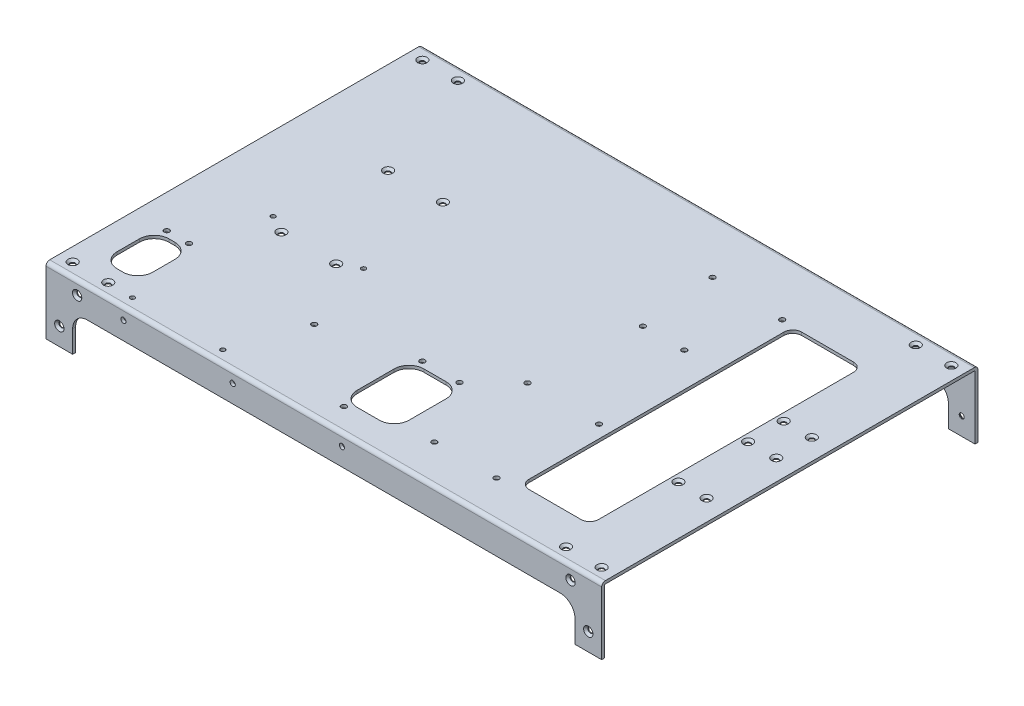
SolidWorks part; units mm, degrees
material "6061-T6 (SS)"
ref_plane "Front Plane" through (0, 0, 0) normal (0, 0, 1) x (1, 0, 0)
ref_plane "Top Plane" through (0, 0, 0) normal (0, 1, 0) x (1, 0, 0)
ref_plane "Right Plane" through (0, 0, 0) normal (1, 0, 0) x (0, 0, -1)
sketch "Sketch1" plane through (0, 0, 0) normal (1, 0, 0) x (0, 0, -1)
  line L0 (125, -100.5) -> (127, -100.5)
  line L1 (-124.5, 0) -> (124.5, 0)
  line L2 (-127, -2.5) -> (-127, -100.5)
  line L3 (-127, -100.5) -> (-125, -100.5)
  line L4 (127, -2.5) -> (127, -100.5)
  line L6 (-125, -100.5) -> (-125, -2.5)
  line L7 (-124.5, -2) -> (124.5, -2)
  line L8 (125, -100.5) -> (125, -2.5)
  arc A0 (-124.5, 0) -> (-127, -2.5) centre (-124.5, -2.5) ccw
  arc A1 (124.5, 0) -> (127, -2.5) centre (124.5, -2.5) cw
  arc A2 (124.5, -2) -> (125, -2.5) centre (124.5, -2.5) cw
  arc A3 (-125, -2.5) -> (-124.5, -2) centre (-124.5, -2.5) cw
  dimension "D1" = 2.5
  dimension "D2" = 250
  dimension "D3" = 2
  dimension "D4" = 100.5
extrude "Boss-Extrude1" add sketch "Sketch1" along normal mid plane 375
sketch "Sketch2" plane through (0, 0, 127) normal (0, 0, 1) x (1, 0, 0)
  line L1 (187.5, -45) -> (187.5, -100.5)
  line L2 (-169.5, -45) -> (-169.5, -30)
  line L3 (-159.5, -20) -> (159.5, -20)
  line L4 (169.5, -45) -> (169.5, -30)
  line L5 (187.5, -2.5) -> (187.5, -100.5) construction
  line L6 (187.5, 0) -> (-187.5, 0) construction
  line L7 (-187.5, -2.5) -> (-187.5, -100.5) construction
  line L8 (169.5, -45) -> (187.5, -45)
  line L9 (187.5, -100.5) -> (-187.5, -100.5)
  line L10 (-187.5, -100.5) -> (-187.5, -45)
  line L11 (-187.5, -45) -> (-169.5, -45)
  arc A0 (159.5, -20) -> (169.5, -30) centre (159.5, -30) cw
  arc A1 (-169.5, -30) -> (-159.5, -20) centre (-159.5, -30) cw
  dimension "D5" = 10
  dimension "D1" = 18
  dimension "D2" = 20
  dimension "D3" = 18
  dimension "D4" = 45
  dimension "D6" = 45
extrude "Cut-Extrude1" cut sketch "Sketch2" against normal through all
sketch "Sketch5" plane through (0, -2, 0) normal (0, -1, 0) x (1, 0, 0)
  line L1 (108.5, 97) -> (143.5, 97)
  line L2 (102.5, 91) -> (102.5, -81)
  line L3 (108.5, -87) -> (143.5, -87)
  line L4 (149.5, 91) -> (149.5, -81)
  line L7 (159.5, -127) -> (-159.5, -127) construction
  line L8 (187.5, 124.5) -> (187.5, -124.5) construction
  line L17 (-187.5, -124.5) -> (-187.5, 124.5) construction
  line L18 (159.5, 127) -> (-159.5, 127) construction
  arc A8 (102.5, -81) -> (108.5, -87) centre (108.5, -81) ccw
  arc A9 (143.5, -87) -> (149.5, -81) centre (143.5, -81) ccw
  arc A10 (149.5, 91) -> (143.5, 97) centre (143.5, 91) ccw
  arc A11 (108.5, 97) -> (102.5, 91) centre (108.5, 91) ccw
  dimension "D5" = 6
  dimension "D1" = 30
  dimension "D2" = 40
  dimension "D3" = 38
  dimension "D4" = 290
extrude "Cut-Extrude4" cut sketch "Sketch5" against normal blind 10
sketch "Sketch6" plane through (0, 0, -127) normal (0, 0, -1) x (-1, 0, 0)
  line L0 (-187.5, 0) -> (187.5, 0) construction
  line L1 (-187.5, -45) -> (-187.5, -2.5) construction
  line L2 (187.5, -45) -> (187.5, -2.5) construction
  circle A0 centre (-178.5, -33) radius 1.5
  circle A1 centre (-178.5, -9) radius 1.5 construction
  circle A2 centre (-166.5, -9) radius 1.5
  circle A3 centre (166.5, -9) radius 1.5
  circle A4 centre (178.5, -9) radius 1.5 construction
  circle A5 centre (178.5, -33) radius 1.5
  dimension "D1" = 3
  dimension "D6" = 9
  dimension "D2" = 9
  dimension "D3" = 9
  dimension "D4" = 33
  dimension "D7" = 21
  dimension "D8" = 21
extrude "Cut-Extrude5" cut sketch "Sketch6" against normal through all
sketch "Sketch9" plane through (0, 0, 0) normal (0, 1, 0) x (1, 0, 0)
  line L0 (-187.5, 124.5) -> (-187.5, -124.5) construction
  line L1 (187.5, 124.5) -> (187.5, -124.5) construction
  line L2 (187.5, 127) -> (-187.5, 127) construction
  line L3 (187.5, -127) -> (-187.5, -127) construction
  circle A0 centre (-178.5, 118) radius 1.5
  circle A1 centre (-154.5, 118) radius 1.5
  circle A2 centre (154.5, 118) radius 1.5
  circle A3 centre (178.5, 118) radius 1.5
  circle A4 centre (178.5, -118) radius 1.5
  circle A5 centre (154.5, -118) radius 1.5
  circle A6 centre (-154.5, -118) radius 1.5
  circle A7 centre (-178.5, -118) radius 1.5
  circle A8 centre (-125.5, 41.85) radius 1.5
  circle A9 centre (-88.5, 41.85) radius 1.5
  circle A10 centre (-125.5, -30.15) radius 1.5
  circle A11 centre (-88.5, -30.15) radius 1.5
  circle A12 centre (154.5, 28.85) radius 1.5
  circle A13 centre (173.5, 4.85) radius 1.5
  circle A14 centre (154.5, 4.85) radius 1.5
  circle A15 centre (173.5, 28.85) radius 1.5
  circle A16 centre (154.5, -42.15) radius 1.5
  circle A17 centre (173.5, -42.15) radius 1.5
  dimension "D1" = 3
  dimension "D2" = 9
  dimension "D3" = 33
  dimension "D4" = 9
  dimension "D5" = 33
  dimension "D6" = 9
  dimension "D7" = 9
extrude "Cut-Extrude8" cut sketch "Sketch9" against normal blind 10
sketch "Sketch19" plane through (0, 0, 0) normal (0, 1, 0) x (1, 0, 0)
  circle A0 centre (-137.5, -23.7) radius 1.5
  circle A2 centre (-76.5, -23.7) radius 1.5
  circle A4 centre (-76.5, -118.7) radius 1.5
  circle A9 centre (-137.5, -118.7) radius 1.5
  dimension "D1" = 3
extrude "Cut-Extrude9" cut sketch "Sketch19" against normal blind 10
sketch "Sketch20" plane through (0, 0, -127) normal (0, 0, -1) x (-1, 0, 0)
  circle A0 centre (-12.25, -8) radius 1.75
  circle A1 centre (61.5, -8) radius 1.75
  circle A2 centre (135.25, -8) radius 1.75
  dimension "D1" = 3.5
extrude "Cut-Extrude10" cut sketch "Sketch20" against normal through all
hole_wizard "CSK for M3 Flat Head Machine Screw1" positions "Sketch22" profile "Sketch21" countersink size "M3" standard "Ansi Metric"
sketch "Sketch22" plane through (0, 0, 127) normal (0, 0, 1) x (1, 0, 0)
  point P0 (-166.5, -9)
  point P1 (166.5, -9)
  point P4 (178.5, -33)
  point P7 (-178.5, -33)
sketch "Sketch21" plane through (-166.5, -9, 127) normal (1, 0, 0) x (0, -1, 0)
  line L0 (0, 0) -> (0, 11.0215)
  line L1 (0, 11.0215) -> (1.7, 10)
  line L2 (1.7, 10) -> (1.7, 1.45)
  line L3 (1.7, 1.45) -> (3.15, 0)
  line L5 (3.15, 0) -> (0, 0)
  line L6 (-1.7, 1.45) -> (-3.15, 0) construction
  line L10 (0, 11.0215) -> (-1.7, 10) construction
  line L11 (0, -6.35) -> (0, 107.95) construction
  dimension "Hole Dia." = 3.4
  dimension "Hole Depth" = 10
  dimension "Near C'Sink Dia." = 6.3
  dimension "Near C'Sink Angle" = 90
  dimension "Drill Angle" = 118
hole_wizard "CSK for M3 Flat Head Machine Screw2" positions "Sketch24" profile "Sketch25" countersink size "M3" standard "Ansi Metric"
sketch "Sketch24" plane through (0, 0, -127) normal (0, 0, -1) x (-1, 0, 0)
  point P0 (-166.5, -9)
  point P1 (178.5, -33)
  point P5 (166.5, -9)
  point P8 (-178.5, -33)
sketch "Sketch25" plane through (166.5, -9, -127) normal (1, 0, 0) x (0, 1, 0)
  line L0 (0, 0) -> (0, 11.0215)
  line L1 (0, 11.0215) -> (1.7, 10)
  line L2 (1.7, 10) -> (1.7, 1.45)
  line L3 (1.7, 1.45) -> (3.15, 0)
  line L5 (3.15, 0) -> (0, 0)
  line L6 (-1.7, 1.45) -> (-3.15, 0) construction
  line L10 (0, 11.0215) -> (-1.7, 10) construction
  line L11 (0, -6.35) -> (0, 107.95) construction
  dimension "Hole Dia." = 3.4
  dimension "Hole Depth" = 10
  dimension "Near C'Sink Dia." = 6.3
  dimension "Near C'Sink Angle" = 90
  dimension "Drill Angle" = 118
hole_wizard "CSK for M3 Flat Head Machine Screw3" positions "Sketch27" profile "Sketch26" countersink size "M3" standard "Ansi Metric"
sketch "Sketch27" plane through (0, 0, 0) normal (0, 1, 0) x (-1, 0, 0)
  point P0 (88.5, -41.85)
  point P1 (178.5, -118)
  point P4 (154.5, -118)
  point P7 (125.5, -41.85)
  point P10 (125.5, 30.15)
  point P13 (88.5, 30.15)
  point P16 (178.5, 118)
  point P19 (154.5, 118)
  point P22 (-154.5, 118)
  point P25 (-178.5, 118)
  point P28 (-154.5, 42.15)
  point P31 (-173.5, 42.15)
  point P34 (-173.5, -4.85)
  point P37 (-154.5, -4.85)
  point P40 (-173.5, -28.85)
  point P43 (-154.5, -28.85)
  point P46 (-178.5, -118)
  point P49 (-154.5, -118)
sketch "Sketch26" plane through (-88.5, 0, -41.85) normal (1, 0, 0) x (0, 0, 1)
  line L0 (0, 0) -> (0, 11.0215)
  line L1 (0, 11.0215) -> (1.7, 10)
  line L2 (1.7, 10) -> (1.7, 1.45)
  line L3 (1.7, 1.45) -> (3.15, 0)
  line L5 (3.15, 0) -> (0, 0)
  line L6 (-1.7, 1.45) -> (-3.15, 0) construction
  line L10 (0, 11.0215) -> (-1.7, 10) construction
  line L11 (0, -6.35) -> (0, 107.95) construction
  dimension "Hole Dia." = 3.4
  dimension "Hole Depth" = 10
  dimension "Near C'Sink Dia." = 6.3
  dimension "Near C'Sink Angle" = 90
  dimension "Drill Angle" = 118
sketch "Sketch28" plane through (0, 0, 0) normal (0, 1, 0) x (-1, 0, 0)
  line L0 (-187.5, 127) -> (187.5, 127) construction
  line L1 (-2.5, 62) -> (-17.5, 62)
  line L2 (7.5, 72) -> (7.5, 97)
  line L3 (-2.5, 107) -> (-17.5, 107)
  line L4 (-27.5, 72) -> (-27.5, 97)
  line L5 (187.5, -124.5) -> (187.5, 124.5) construction
  line L6 (150, 68) -> (165, 68) construction
  line L7 (155.5, 107) -> (159.5, 107)
  line L8 (145.5, 97) -> (145.5, 82)
  line L9 (155.5, 72) -> (159.5, 72)
  line L10 (169.5, 97) -> (169.5, 82)
  line L11 (157.5, 68) -> (157.5, 72) construction
  arc A0 (-17.5, 107) -> (-27.5, 97) centre (-17.5, 97) ccw
  arc A1 (-17.5, 62) -> (-27.5, 72) centre (-17.5, 72) cw
  arc A2 (-2.5, 62) -> (7.5, 72) centre (-2.5, 72) ccw
  arc A3 (7.5, 97) -> (-2.5, 107) centre (-2.5, 97) ccw
  circle A4 centre (2.5, 111) radius 1.75
  arc A5 (159.5, 72) -> (169.5, 82) centre (159.5, 82) ccw
  arc A6 (145.5, 82) -> (155.5, 72) centre (155.5, 82) ccw
  arc A7 (155.5, 107) -> (145.5, 97) centre (155.5, 97) ccw
  arc A8 (159.5, 107) -> (169.5, 97) centre (159.5, 97) cw
  circle A9 centre (2.5, 58) radius 1.75
  circle A10 centre (-22.5, 58) radius 1.75
  circle A11 centre (150, 68) radius 1.75
  circle A12 centre (165, 68) radius 1.75
  dimension "D5" = 10
  dimension "D6" = 4
  dimension "D8" = 5
  dimension "D9" = 10
  dimension "D14" = 3.5
  dimension "D1" = 20
  dimension "D2" = 45
  dimension "D3" = 180
  dimension "D4" = 215
  dimension "D7" = 4
  dimension "D10" = 18
  dimension "D11" = 20
  dimension "D12" = 24
  dimension "D13" = 35
  dimension "D15" = 5
  dimension "D16" = 15
  dimension "D17" = 4
extrude "Cut-Extrude11" cut sketch "Sketch28" against normal blind 10
sketch "Sketch29" plane through (0, -2, 0) normal (0, -1, 0) x (1, 0, 0)
  circle A0 centre (48.8761, 101.2613) radius 1.75
  circle A1 centre (90.7861, 101.2538) radius 1.75
  circle A2 centre (45.6892, 35.2219) radius 1.75
  circle A3 centre (93.9492, 35.2132) radius 1.75
  circle A4 centre (51.527, -36.839) radius 1.75
  circle A5 centre (79.467, -36.839) radius 1.75
  circle A6 centre (46.447, -88.91) radius 1.75
  circle A7 centre (94.707, -87.639) radius 1.75
  dimension "D1" = 3.5
extrude "Cut-Extrude12" cut sketch "Sketch29" against normal blind 10
sketch "Sketch30" plane through (0, -2, 0) normal (0, -1, 0) x (1, 0, 0)
  line L0 (-187.5, 124.5) -> (-187.5, -124.5) construction
  line L2 (159.5, 127) -> (-159.5, 127) construction
  circle A0 centre (-60.5, 73) radius 1.75
  dimension "D3" = 3.5
  dimension "D1" = 127
  dimension "D2" = 54
extrude "Cut-Extrude13" cut sketch "Sketch30" against normal through all
